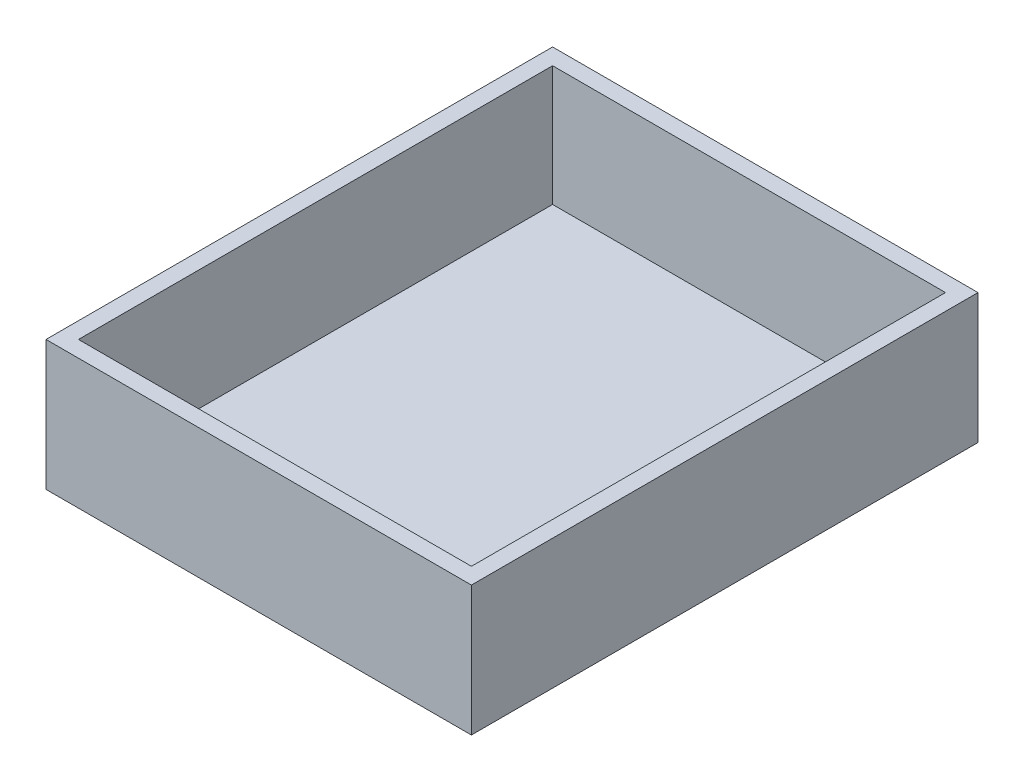
SolidWorks part; units mm, degrees
ref_plane "Plano frontal" through (0, 0, 0) normal (0, 0, 1) x (1, 0, 0)
ref_plane "Plano superior" through (0, 0, 0) normal (0, 1, 0) x (1, 0, 0)
ref_plane "Plano direito" through (0, 0, 0) normal (1, 0, 0) x (0, 0, -1)
sketch "Esboço1" plane through (0, 0, 0) normal (0, 1, 0) x (-1, 0, 0)
  line L8 (-65.5, -78) -> (65.5, -78)
  line L9 (65.5, -78) -> (65.5, 78)
  line L10 (65.5, 78) -> (-65.5, 78)
  line L11 (-65.5, 78) -> (-65.5, -78)
  point P2 (0, 78)
  point P4 (65.5, 0)
  dimension "D1" = 156
  dimension "D2" = 131
extrude "Ressalto-extrusão1" add sketch "Esboço1" along normal blind 40
sketch "Esboço3" plane through (0, 40, 0) normal (0, 1, 0) x (1, 0, 0)
  line L8 (60.5, -73) -> (60.5, 73)
  line L9 (60.5, 73) -> (-60.5, 73)
  line L10 (-60.5, 73) -> (-60.5, -73)
  line L11 (-60.5, -73) -> (60.5, -73)
  line L12 (60.5, -73) -> (60.5, 73)
  line L13 (60.5, 73) -> (-60.5, 73)
  line L14 (-60.5, 73) -> (-60.5, -73)
  line L15 (-60.5, -73) -> (60.5, -73)
  dimension "D1" = 5
extrude "Corte-extrusão1" cut sketch "Esboço3" against normal blind 37
